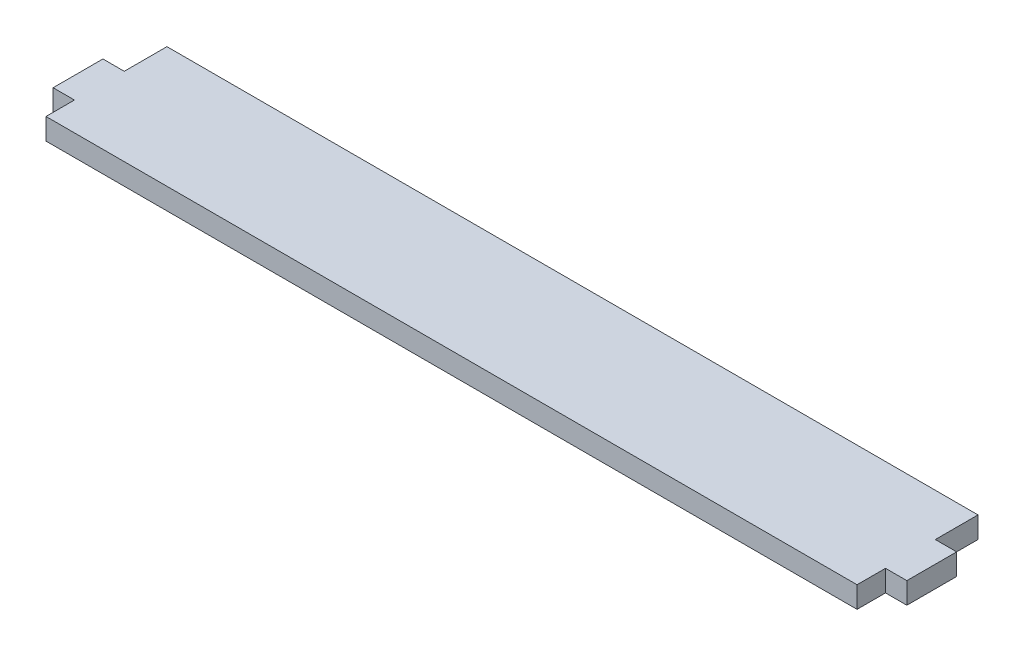
SolidWorks part; units mm, degrees
ref_plane "Alzado" through (0, 0, 0) normal (0, 0, 1) x (1, 0, 0)
ref_plane "Planta" through (0, 0, 0) normal (0, 1, 0) x (1, 0, 0)
ref_plane "Vista lateral" through (0, 0, 0) normal (1, 0, 0) x (0, 0, -1)
sketch "Croquis1" plane through (0, 0, 0) normal (0, 1, 0) x (1, 0, 0)
  line L0 (-57, 2.5) -> (-60, 2.5)
  line L1 (57, -8.5) -> (-57, -8.5)
  line L2 (57, -8.5) -> (57, -4.5)
  line L3 (57, 8.5) -> (-57, 8.5)
  line L4 (-57, -8.5) -> (-57, -4.5)
  line L5 (57, -8.5) -> (-57, 8.5) construction
  line L6 (57, 8.5) -> (-57, -8.5) construction
  line L7 (-60, 2.5) -> (-60, -4.5)
  line L8 (-60, -4.5) -> (-57, -4.5)
  line L9 (0, 0) -> (0, -21.1167) construction
  line L10 (60, -4.5) -> (57, -4.5)
  line L11 (60, 2.5) -> (60, -4.5)
  line L12 (57, 2.5) -> (60, 2.5)
  line L13 (-57, 2.5) -> (-57, 8.5)
  line L14 (57, 2.5) -> (57, 8.5)
  point P0 (0, 0)
  dimension "D1" = 17
  dimension "D2" = 3
  dimension "D3" = 6
  dimension "D4" = 7
  dimension "D5" = 120
extrude "Saliente-Extruir1" add sketch "Croquis1" along normal blind 3
